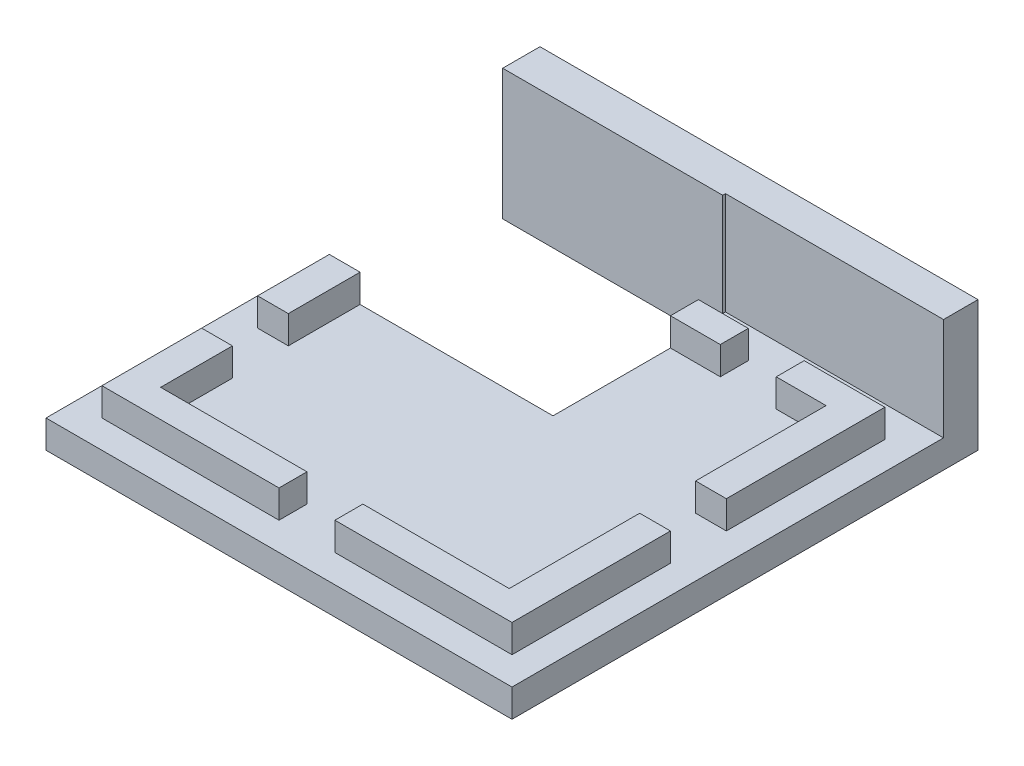
SolidWorks part; units mm, degrees
ref_plane "Front Plane" through (0, 0, 0) normal (0, 0, 1) x (1, 0, 0)
ref_plane "Top Plane" through (0, 0, 0) normal (0, 1, 0) x (1, 0, 0)
ref_plane "Right Plane" through (0, 0, 0) normal (1, 0, 0) x (0, 0, -1)
sketch "Sketch1" plane through (0, 0, 0) normal (0, 1, 0) x (1, 0, 0)
  line L1 (-12.5, -11.5) -> (12.5, -11.5)
  line L2 (-12.5, -11.5) -> (-12.5, 11.5)
  line L3 (-12.5, 11.5) -> (12.5, 11.5)
  line L4 (12.5, -11.5) -> (12.5, 11.5)
  line L5 (-12.5, -11.5) -> (12.5, 11.5) construction
  line L6 (-12.5, 11.5) -> (12.5, -11.5) construction
  point P0 (0, 0)
  dimension "D1" = 25
  dimension "D2" = 23
extrude "Boss-Extrude1" add sketch "Sketch1" along normal blind 1.5
sketch "Sketch2" plane through (0, 1.5, 0) normal (0, 1, 0) x (1, 0, 0)
  line L0 (12.5, 11.5) -> (-12.5, 11.5) construction
  line L1 (-11, -10) -> (11, -10)
  line L2 (-11, -10) -> (-11, 10)
  line L3 (-11, 10) -> (11, 10)
  line L4 (11, -10) -> (11, 10)
  line L5 (-11, -10) -> (11, 10) construction
  line L6 (-11, 10) -> (11, -10) construction
  line L7 (-12.5, 11.5) -> (-12.5, -11.5) construction
  line L9 (-9.35, -8.5) -> (9.35, -8.5)
  line L10 (-9.35, -8.5) -> (-9.35, 8.5)
  line L11 (-9.35, 8.5) -> (9.35, 8.5)
  line L12 (9.35, -8.5) -> (9.35, 8.5)
  line L13 (-9.35, -8.5) -> (9.35, 8.5) construction
  line L14 (-9.35, 8.5) -> (9.35, -8.5) construction
  point P0 (0, 0)
  point P10 (0, 0)
  dimension "D1" = 1.5
  dimension "D2" = 1.5
  dimension "D3" = 1.5
extrude "Boss-Extrude2" add sketch "Sketch2" along normal blind 1.5
sketch "Sketch4" plane through (0, 1.5, 0) normal (0, 1, 0) x (1, 0, 0)
  line L0 (-11, -10) -> (11, -10) construction
  line L1 (-11, 10) -> (1, 10)
  line L2 (-11, 10) -> (-11, 2.2)
  line L3 (-11, 2.2) -> (1, 2.2)
  line L4 (1, 10) -> (1, 2.2)
  line L5 (12.5, 11.5) -> (-12.5, 11.5) construction
  line L6 (-12.5, 11.5) -> (-12.5, -11.5) construction
  dimension "D1" = 12.2
  dimension "D2" = 1.5
  dimension "D3" = 1.5
  dimension "D4" = 12
extrude "Cut-Extrude2" cut sketch "Sketch4" against normal through all and the other way through all contours L2 L1 L4 L3
sketch "Sketch5" plane through (0, 0, 0) normal (0, -1, 0) x (1, 0, 0)
  line L1 (1, -2.2) -> (-12.5, -2.2)
  line L2 (1, -2.2) -> (1, -11.5)
  line L3 (1, -11.5) -> (-12.5, -11.5)
  line L4 (-12.5, -2.2) -> (-12.5, -11.5)
extrude "Cut-Extrude3" cut sketch "Sketch5" against normal through all
sketch "Sketch6" plane through (0, 3, 0) normal (0, 1, 0) x (1, 0, 0)
  line L0 (-11, 2.2) -> (-11, -10) construction
  line L1 (-11, -1.65) -> (-9.35, -1.65)
  line L2 (-11, -1.65) -> (-11, -4.65)
  line L3 (-11, -4.65) -> (-9.35, -4.65)
  line L4 (-9.35, -1.65) -> (-9.35, -4.65)
  line L5 (-9.35, 2.2) -> (-9.35, -8.5) construction
  line L6 (-9.35, -8.5) -> (9.35, -8.5) construction
  line L7 (-1.5, -8.5) -> (1.5, -8.5)
  line L8 (-1.5, -8.5) -> (-1.5, -10)
  line L9 (-1.5, -10) -> (1.5, -10)
  line L10 (1.5, -8.5) -> (1.5, -10)
  line L11 (-11, -10) -> (11, -10) construction
  line L12 (9.35, -8.5) -> (9.35, 8.5) construction
  line L13 (9.35, 1.5) -> (11, 1.5)
  line L14 (9.35, 1.5) -> (9.35, -1.5)
  line L15 (9.35, -1.5) -> (11, -1.5)
  line L16 (11, 1.5) -> (11, -1.5)
  line L17 (11, -10) -> (11, 10) construction
  line L18 (11, 10) -> (1, 10) construction
  line L19 (3.675, 10) -> (6.675, 10)
  line L20 (3.675, 10) -> (3.675, 8.5)
  line L21 (3.675, 8.5) -> (6.675, 8.5)
  line L22 (6.675, 10) -> (6.675, 8.5)
  line L23 (9.35, 8.5) -> (1, 8.5) construction
  line L24 (9.35, -8.5) -> (9.35, 8.5) construction
  point P32 (5.175, 10)
  point P36 (-11, -3.15)
  dimension "D1" = 3
  dimension "D2" = 3
  dimension "D3" = 3
  dimension "D4" = 3
  dimension "D5" = 4.175
  dimension "D6" = 1.5
  dimension "D7" = 1.5
  dimension "D8" = 5.35
extrude "Cut-Extrude4" cut sketch "Sketch6" against normal up to surface (1.5 mm away) up to face at (0.3333, 1.5, -0.7333)
sketch "Sketch7" plane through (0, 0, -11.5) normal (0, 0, -1) x (-1, 0, 0)
  line L0 (-12.5, 1.5) -> (-12.5, 0) construction
  line L1 (-12.5, 0) -> (11, 0)
  line L2 (-12.5, 0) -> (-12.5, 7)
  line L3 (-12.5, 7) -> (11, 7)
  line L4 (11, 0) -> (11, 7)
  dimension "D1" = 7
extrude "Boss-Extrude3" add sketch "Sketch7" along normal blind 2
sketch "Sketch8" plane through (0, 7, 0) normal (0, 1, 0) x (1, 0, 0)
  line L0 (-11, 11.5) -> (12.5, 11.5) construction
  line L1 (12.5, 11.5) -> (0.8, 11.5)
  line L2 (12.5, 11.5) -> (12.5, 11.65)
  line L3 (12.5, 11.65) -> (0.8, 11.65)
  line L4 (0.8, 11.5) -> (0.8, 11.65)
  line L5 (12.5, 13.5) -> (12.5, 11.5) construction
  dimension "D1" = 0.15
  dimension "D2" = 11.7
extrude "Cut-Extrude5" cut sketch "Sketch8" against normal up to surface (5.5 mm away) up to face at (-2.0964, 1.5, -3.0357)
